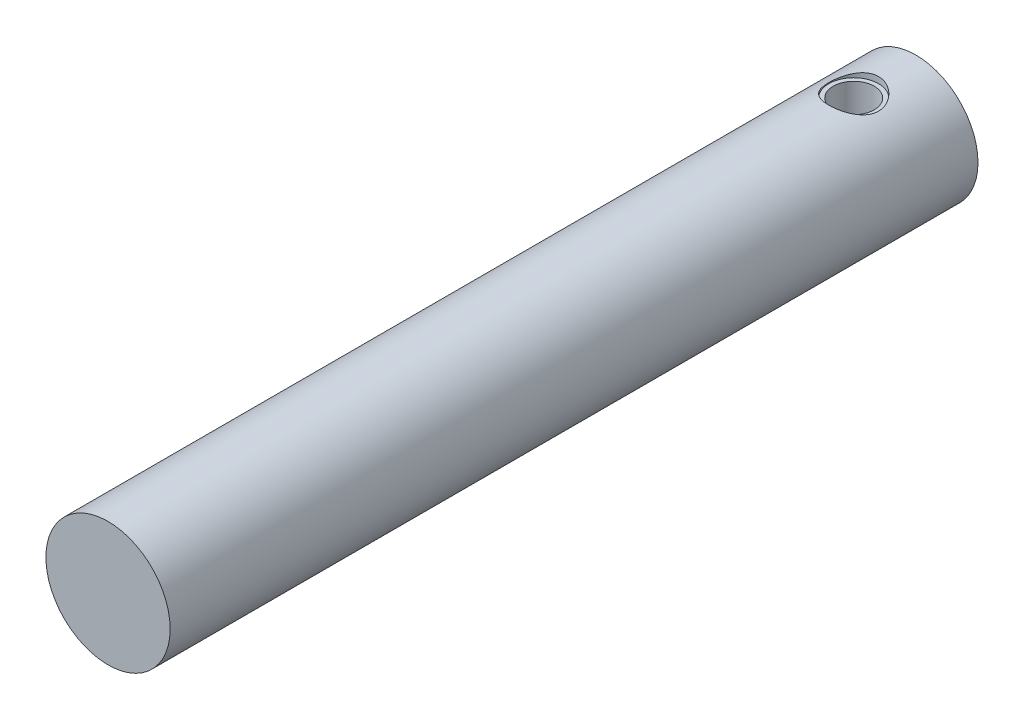
SolidWorks part; units mm, degrees
material "1060 合金"
ref_plane "前基準面" through (0, 0, 0) normal (0, 0, 1) x (1, 0, 0)
ref_plane "上基準面" through (0, 0, 0) normal (0, 1, 0) x (1, 0, 0)
ref_plane "右基準面" through (0, 0, 0) normal (1, 0, 0) x (0, 0, -1)
sketch "草圖1" plane through (0, 0, 0) normal (0, 1, 0) x (1, 0, 0)
  line L0 (0, -16.7467) -> (0, 78.4448) construction
  line L1 (0, 0) -> (5, 0)
  line L2 (0, 0) -> (0, 65)
  line L3 (0, 65) -> (5, 65)
  line L4 (5, 0) -> (5, 65)
  line L5 (0, -5.5) -> (0, 5.5) construction
  dimension "D1" = 10
  dimension "D2" = 65
revolve "旋轉1" add sketch "草圖1" angle 360 about L0
ref_plane "平面1" through (0, 5, 0) normal (0, 1, 0) x (1, 0, 0)
sketch "草圖2" plane through (0, 5, 0) normal (0, 1, 0) x (1, 0, 0)
  line L0 (0, -5.5) -> (0, 5.5) construction
  line L1 (5, 65) -> (-5, 65) construction
  circle A0 centre (0, 60) radius 2
  point P7 (0, 60)
  dimension "D1" = 5
  dimension "D2" = 4
extrude "除料-伸長1" cut sketch "草圖2" against normal blind 0.5
hole_wizard "M4 螺紋孔2" positions "3D草圖6" profile "草圖8" tap size "M4" standard "ISO"
sketch3d "3D草圖6"
  line L0 (0, 4.5, -60) -> (0, 5, -60) construction
  point P0 (0, 4.5, -60)
sketch "草圖8" plane through (0, 4.5, -60) normal (1, 0, 0) x (0, 0, 1)
  line L0 (0, 0) -> (0, 5.9914)
  line L1 (0, 5.9914) -> (1.65, 5)
  line L2 (1.65, 5) -> (1.65, 0)
  line L5 (1.65, 0) -> (0, 0)
  line L10 (0, 5.9914) -> (-1.65, 5) construction
  line L11 (0, -6.35) -> (0, 107.95) construction
  dimension "螺孔鑽直徑" = 3.3
  dimension "螺孔鑽深度" = 5
  dimension "導頭角度" = 118
cosmetic thread "鑽孔螺紋2"
